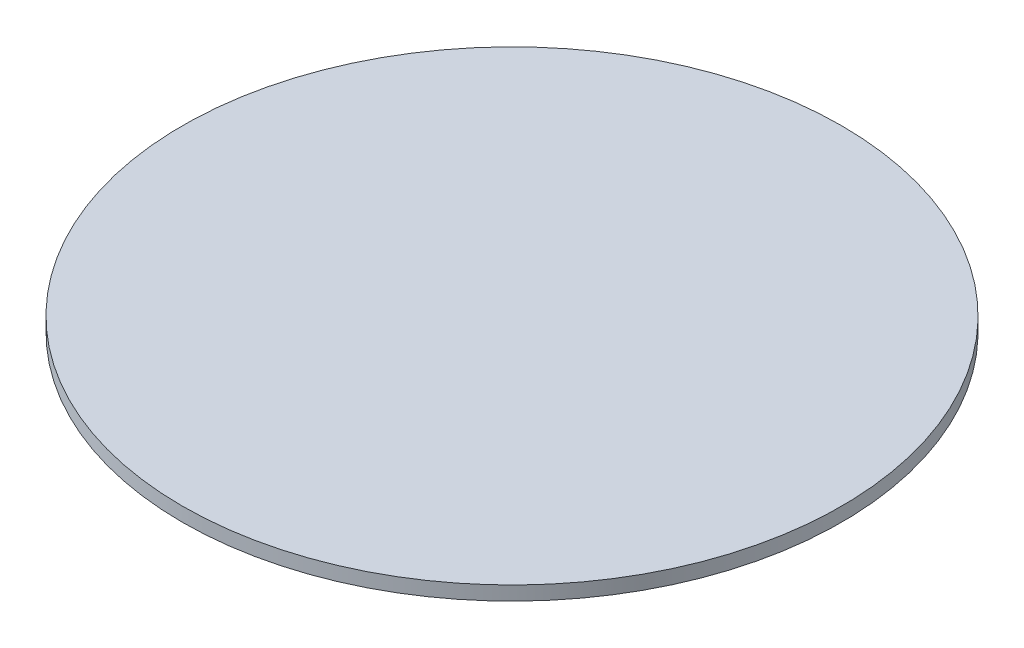
SolidWorks part; units mm, degrees
ref_plane "Front Plane" through (0, 0, 0) normal (0, 0, 1) x (1, 0, 0)
ref_plane "Top Plane" through (0, 0, 0) normal (0, 1, 0) x (1, 0, 0)
ref_plane "Right Plane" through (0, 0, 0) normal (1, 0, 0) x (0, 0, -1)
sketch "Sketch1" plane through (0, 0, 0) normal (0, 1, 0) x (1, 0, 0)
  circle A0 centre (0, 0) radius 40
extrude "Boss-Extrude1" add sketch "Sketch1" along normal blind 1.7
